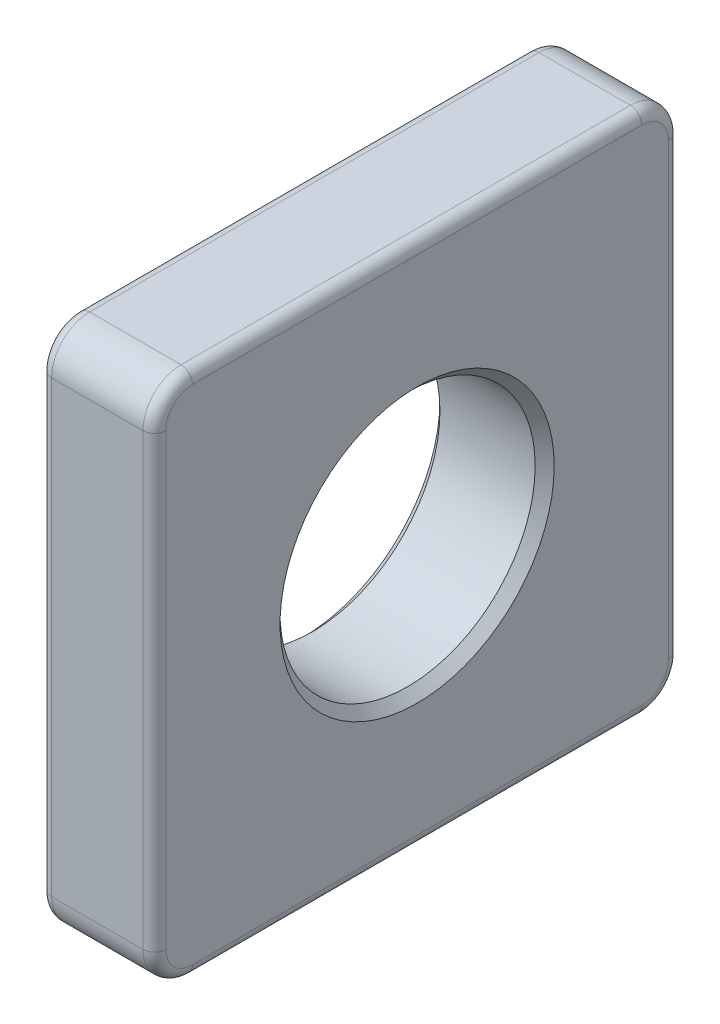
SolidWorks part; units mm, degrees
ref_plane "Front" through (0, 0, 0) normal (0, 0, 1) x (1, 0, 0)
ref_plane "Top" through (0, 0, 0) normal (0, 1, 0) x (1, 0, 0)
ref_plane "Right" through (0, 0, 0) normal (1, 0, 0) x (0, 0, -1)
sketch "Sketch1" plane through (0, 0, 0) normal (1, 0, 0) x (0, 0, -1)
  line L1 (6.9, -6.9) -> (-6.9, -6.9)
  line L2 (6.9, -6.9) -> (6.9, 6.9)
  line L3 (6.9, 6.9) -> (-6.9, 6.9)
  line L4 (-6.9, -6.9) -> (-6.9, 6.9)
  line L5 (6.9, -6.9) -> (-6.9, 6.9) construction
  line L6 (6.9, 6.9) -> (-6.9, -6.9) construction
  point P0 (0, 0)
  dimension "D1" = 6.9
  dimension "D2" = 13.8
extrude "Boss-Extrude1" add sketch "Sketch1" along normal blind 3
sketch "Sketch2" plane through (0, 0, 0) normal (1, 0, 0) x (0, 0, -1)
  circle A0 centre (0, 0) radius 3.35
  dimension "D1" = 6.7
extrude "Cut-Extrude1" cut sketch "Sketch2" along normal through all
chamfer "Chamfer1" distance 0.25 angle 45 2 edges at (0, 0, -3.35) (3, 0, -3.35)
fillet "Fillet1" radius 1 4 edges at (1.5, 6.9, -6.9) (1.5, -6.9, -6.9) (1.5, -6.9, 6.9) (1.5, 6.9, 6.9)
fillet "Fillet2" radius 0.3 16 edges at (0, 6.6071, 6.6071) (0, 6.9, 0) (0, 6.6071, -6.6071) (0, 0, -6.9) (0, -6.6071, -6.6071) (0, -6.9, 0) (0, -6.6071, 6.6071) (3, -6.6071, 6.6071) (3, 0, 6.9) (3, 6.6071, 6.6071) (3, 6.9, 0) (3, 6.6071, -6.6071) (3, 0, -6.9) (3, -6.6071, -6.6071) (0, 0, 6.9) (3, -6.9, 0)
equation "\"D2@Sketch1\"=2*\"D1@Sketch1\""
